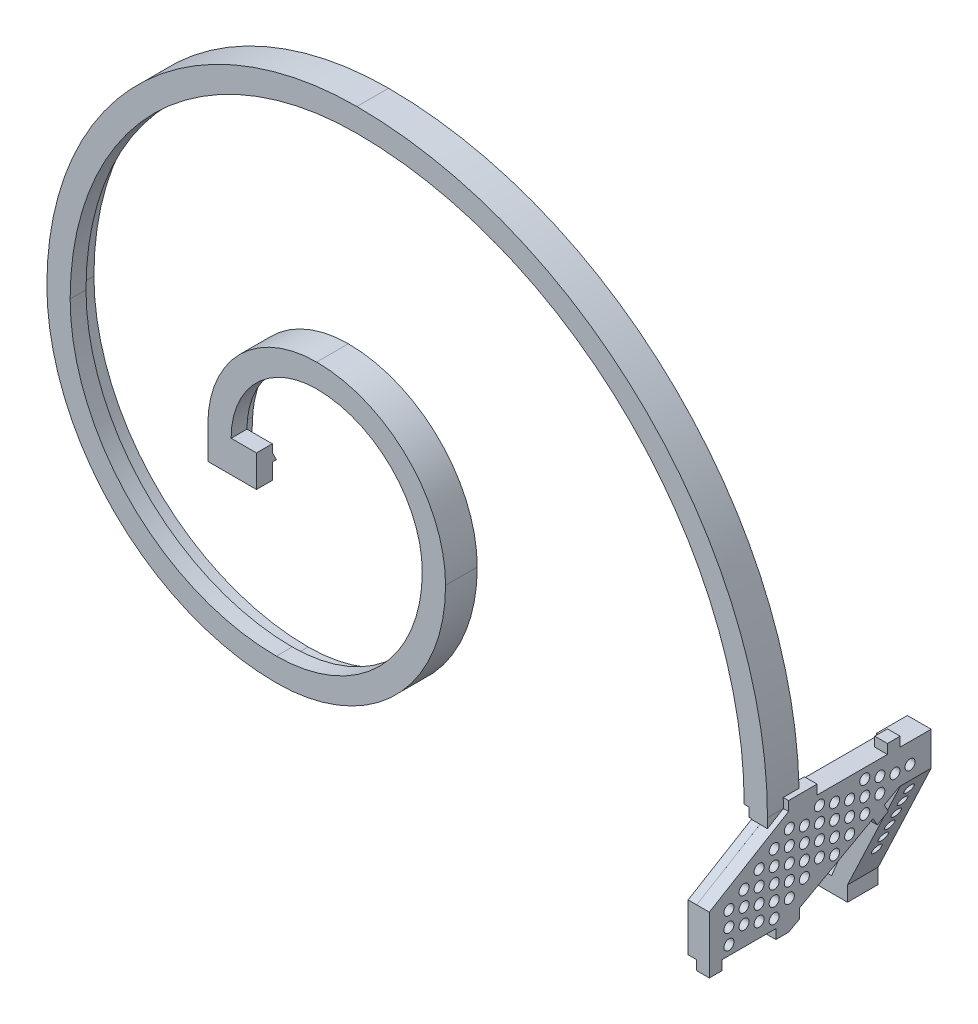
SolidWorks part; units mm, degrees
ref_plane "Front" through (0, 0, 0) normal (0, 0, 1) x (1, 0, 0)
ref_plane "Top" through (0, 0, 0) normal (0, 1, 0) x (1, 0, 0)
ref_plane "Right" through (0, 0, 0) normal (1, 0, 0) x (0, 0, -1)
sketch "Sketch2" plane through (0, 0, 0) normal (0, 0, 1) x (1, 0, 0)
  line L0 (-28.4875, 0) -> (-28.4875, -10)
  line L1 (-28.4875, -10) -> (-31.9875, -10)
  line L2 (-31.9875, -10) -> (-31.9875, 0)
  line L3 (139.9375, -19.05) -> (136.4375, -19.05)
  arc A0 (-28.4875, 0) -> (0, 28.4875) centre (0, 0) cw
  arc A1 (0, 28.4875) -> (34.8375, -6.35) centre (0, -6.35) cw
  arc A2 (34.8375, -6.35) -> (-12.7, -53.8875) centre (-12.7, -6.35) cw
  arc A3 (-12.7, -53.8875) -> (-79.2875, 12.7) centre (-12.7, 12.7) cw
  arc A4 (-79.2875, 12.7) -> (12.7, 104.6875) centre (12.7, 12.7) cw
  arc A5 (12.7, 104.6875) -> (136.4375, -19.05) centre (12.7, -19.05) cw
  arc A6 (-31.9875, 0) -> (0, 31.9875) centre (0, 0) cw
  arc A7 (0, 31.9875) -> (38.3375, -6.35) centre (0, -6.35) cw
  arc A8 (38.3375, -6.35) -> (-12.7, -57.3875) centre (-12.7, -6.35) cw
  arc A9 (-12.7, -57.3875) -> (-82.7875, 12.7) centre (-12.7, 12.7) cw
  arc A10 (-82.7875, 12.7) -> (12.7, 108.1875) centre (12.7, 12.7) cw
  arc A11 (12.7, 108.1875) -> (139.9375, -19.05) centre (12.7, -19.05) cw
extrude "Extrude2" add sketch "Sketch2" along normal blind 5
sketch "Sketch3" plane through (0, 0, 5) normal (0, 0, 1) x (1, 0, 0)
  line L0 (-26.9875, 0) -> (-26.9875, -10)
  line L1 (-26.9875, -10) -> (-31.9875, -10)
  line L2 (134.9375, -19.05) -> (139.9375, -19.05)
  line L3 (-31.9875, -10) -> (-31.9875, 0)
  arc A0 (-31.9875, 0) -> (0, 31.9875) centre (0, 0) cw
  arc A1 (-26.9875, 0) -> (0, 26.9875) centre (0, 0) cw
  arc A2 (0, 26.9875) -> (33.3375, -6.35) centre (0, -6.35) cw
  arc A3 (0, 31.9875) -> (38.3375, -6.35) centre (0, -6.35) cw
  arc A5 (33.3375, -6.35) -> (-12.7, -52.3875) centre (-12.7, -6.35) cw
  arc A6 (-12.7, -52.3875) -> (-77.7875, 12.7) centre (-12.7, 12.7) cw
  arc A7 (-77.7875, 12.7) -> (12.7, 103.1875) centre (12.7, 12.7) cw
  arc A8 (12.7, 103.1875) -> (134.9375, -19.05) centre (12.7, -19.05) cw
  arc A9 (38.3375, -6.35) -> (-12.7, -57.3875) centre (-12.7, -6.35) cw
  arc A10 (-12.7, -57.3875) -> (-82.7875, 12.7) centre (-12.7, 12.7) cw
  arc A11 (-82.7875, 12.7) -> (-12.7, -57.3875) centre (-12.7, 12.7) ccw construction
  arc A12 (-82.7875, 12.7) -> (12.7, 108.1875) centre (12.7, 12.7) cw
  arc A13 (12.7, 108.1875) -> (139.9375, -19.05) centre (12.7, -19.05) cw
extrude "Extrude3" add sketch "Sketch3" along normal blind 5
sketch "Sketch4" plane through (-28.4875, 0, 0) normal (1, 0, 0) x (0, 0, -1)
  line L0 (-5, -2.4) -> (-1.2, -10)
  line L1 (-5, -19.05) -> (-5, 104.6875) construction
  line L2 (-5, -10) -> (0, -10) construction
  line L3 (-1.2, -10) -> (-5, -10)
  line L4 (-5, -10) -> (-5, -2.4)
extrude "Extrude4" add sketch "Sketch4" along normal blind 9.5
sketch "Sketch6" plane through (-18.9875, 0, 0) normal (1, 0, 0) x (0, 0, -1)
  line L0 (-5, -5) -> (-3.7, -5)
  line L1 (-5, -19.05) -> (-5, 104.6875) construction
  line L2 (-1.2, -10) -> (-5, -2.4) construction
  line L3 (-3.7, -5) -> (-1.2, -10)
  line L4 (-1.2, -10) -> (-5, -10)
  line L5 (-5, -10) -> (-5, -5)
extrude "Cut-Extrude1" cut sketch "Sketch6" against normal blind 8
sketch "Sketch7" plane through (-26.9875, 0, 0) normal (1, 0, 0) x (0, 0, -1)
  line L0 (-5, 0) -> (-10, 0)
  line L1 (-10, 0) -> (-10, -10)
  line L2 (-10, -10) -> (-5, -10)
  line L3 (-5, -19.05) -> (-5, 104.6875) construction
  line L4 (-5, -10) -> (-5, 0)
extrude "Extrude5" add sketch "Sketch7" along normal blind 8
sketch "Sketch8" plane through (0, -19.05, 0) normal (0, -1, 0) x (1, 0, 0)
  line L0 (139.9375, 10) -> (139.9375, 0)
  line L1 (139.9375, 0) -> (136.4375, 0)
  line L2 (136.4375, 0) -> (136.4375, 10)
  line L3 (134.9375, 10) -> (139.9375, 10) construction
  line L4 (136.4375, 10) -> (139.9375, 10)
extrude "Extrude6" add sketch "Sketch8" along normal blind 30
sketch "Sketch9" plane through (0, 0, 10) normal (0, 0, 1) x (1, 0, 0)
  line L0 (136.4375, -19.05) -> (139.9375, -19.05)
  line L1 (139.9375, -19.05) -> (139.9375, -49.05)
  line L2 (139.9375, -49.05) -> (136.4375, -49.05)
  line L3 (136.4375, -49.05) -> (136.4375, -19.05)
extrude "Extrude7" add sketch "Sketch9" along normal blind 20
sketch "Sketch11" plane through (0, 0, 0) normal (0, 0, -1) x (-1, 0, 0)
  line L0 (-139.9375, -19.05) -> (-136.4375, -19.05)
  line L1 (-136.4375, -19.05) -> (-136.4375, -49.05)
  line L2 (-136.4375, -49.05) -> (-139.9375, -49.05)
  line L3 (-139.9375, -49.05) -> (-139.9375, -19.05)
extrude "Extrude8" add sketch "Sketch11" along normal blind 30
sketch "Sketch10" plane through (139.9375, 0, 0) normal (1, 0, 0) x (0, 0, -1)
  line L0 (-5, -49.05) -> (30, -29.7287)
  line L1 (-30, -49.05) -> (-30, -19.05) construction
  line L2 (30, -49.05) -> (-30, -49.05) construction
  line L3 (-30, -34.05) -> (-30, -19.05)
  line L4 (-30, -19.05) -> (-10, -19.05)
  line L5 (-10, -19.05) -> (-10, -22.05)
  line L6 (-10, -22.05) -> (-30, -34.05)
  line L7 (30, -19.05) -> (30, -49.05) construction
  line L8 (30, -29.7287) -> (30, -49.05)
  line L9 (30, -49.05) -> (-5, -49.05)
extrude "Cut-Extrude2" cut sketch "Sketch10" against normal blind 5
sketch "Sketch12" plane through (0, 0, -30) normal (0, 0, -1) x (-1, 0, 0)
  line L0 (-139.9375, -19.05) -> (-136.4375, -19.05)
  line L1 (-136.4375, -19.05) -> (-136.4375, -29.7287)
  line L2 (-139.9375, -19.05) -> (-139.9375, -29.7287)
  line L4 (-136.4375, -29.7287) -> (-139.9375, -29.7287)
extrude "Extrude9" add sketch "Sketch12" along normal blind 10
sketch "Sketch14" plane through (0, 0, 10) normal (0, 0, 1) x (1, 0, 0)
  line L0 (-34.3375, 0) -> (-34.3375, -10)
  line L1 (-31.9875, 0) -> (-31.9875, -10)
  line L2 (-31.9875, 0) -> (-31.9875, -10) construction
  line L3 (-31.9875, -10) -> (-34.3375, -10)
  line L4 (142.2875, -19.0647) -> (142.2875, -34.05)
  line L5 (142.2875, -34.05) -> (139.9375, -34.05)
  line L6 (139.9375, -34.05) -> (139.9375, -19.0647)
  arc A0 (-34.3375, 0) -> (0, 34.3375) centre (0, 0) cw
  arc A1 (0, 34.3375) -> (40.6875, -6.35) centre (0, -6.35) cw
  arc A2 (40.6875, -6.35) -> (-12.7, -59.7375) centre (-12.7, -6.35) cw
  arc A3 (-12.7, -59.7375) -> (-85.1375, 12.7419) centre (-12.7, 12.7) cw
  arc A4 (-31.9875, 0) -> (0, 31.9875) centre (0, 0) cw
  arc A5 (0, 31.9875) -> (38.3375, -6.35) centre (0, -6.35) cw
  arc A6 (38.3375, -6.35) -> (-12.7, -57.3875) centre (-12.7, -6.35) cw
  arc A7 (-12.7, -57.3875) -> (-82.7875, 12.7406) centre (-12.7, 12.7) cw
  arc A8 (-82.7875, 12.7406) -> (12.7, 108.1728) centre (12.7, 12.6853) cw
  arc A9 (-85.1375, 12.7419) -> (12.7, 110.5228) centre (12.7, 12.6853) cw
  arc A10 (12.7, 108.1728) -> (139.9375, -19.0647) centre (12.7, -19.0647) cw
  arc A11 (12.7, 110.5228) -> (142.2875, -19.0647) centre (12.7, -19.0647) cw
extrude "Extrude10" add sketch "Sketch14" against normal blind 10
sketch "Sketch15" plane through (-34.3375, 0, 0) normal (-1, 0, 0) x (0, 0, 1)
  line L0 (0, 14) -> (0, -10)
  line L1 (0, 110.5228) -> (0, 12.7419) construction
  line L2 (0, -10) -> (1.2, -10)
  line L3 (1.2, -10) -> (0, 14)
extrude "Cut-Extrude3" cut sketch "Sketch15" against normal blind 15
sketch "Sketch16" plane through (0, 0, 0) normal (0, 0, -1) x (-1, 0, 0)
  line L0 (28.4875, 0) -> (29.4875, 0)
  line L1 (-137.4375, -19.05) -> (-136.4375, -34.05)
  line L4 (-136.4375, -34.05) -> (-136.4375, -19.05)
  arc A0 (28.4875, 0) -> (0, 28.4875) centre (0, 0) ccw
  arc A1 (0, 28.4875) -> (-34.8375, -6.35) centre (0, -6.35) ccw
  arc A2 (-34.8375, -6.35) -> (12.7, -53.8875) centre (12.7, -6.35) ccw
  arc A3 (12.7, -53.8875) -> (79.2875, 12.7) centre (12.7, 12.7) ccw
  arc A4 (79.2875, 12.7) -> (-12.7, 104.6875) centre (-12.7, 12.7) ccw
  arc A5 (-12.7, 104.6875) -> (-136.4375, -19.05) centre (-12.7, -19.05) ccw
  arc A6 (29.4875, 0) -> (0, 29.4875) centre (0, 0) ccw
  arc A7 (0, 29.4875) -> (-35.8375, -6.35) centre (0, -6.35) ccw
  arc A8 (-35.8375, -6.35) -> (12.7, -54.8875) centre (12.7, -6.35) ccw
  arc A9 (12.7, -54.8875) -> (80.2875, 12.7) centre (12.7, 12.7) ccw
  arc A10 (80.2875, 12.7) -> (-12.7, 105.6875) centre (-12.7, 12.7) ccw
  arc A11 (-12.7, 105.6875) -> (-137.4375, -19.05) centre (-12.7, -19.05) ccw
extrude "Cut-Extrude4" cut sketch "Sketch16" against normal blind 5
sketch "Sketch17" plane through (-28.4875, 0, 0) normal (1, 0, 0) x (0, 0, -1)
  line L0 (-5, 0) -> (-5, -2.4)
  line L1 (-5, -2.4) -> (-1.2, -10)
  line L2 (-1.2, -10) -> (0, -10)
  line L3 (0, -19.0647) -> (0, 110.5228) construction
  line L4 (0, -10) -> (0, 0)
  line L5 (0, 0) -> (-5, 0)
extrude "Cut-Extrude5" cut sketch "Sketch17" against normal blind 1
sketch "Sketch19" plane through (136.4375, 0, 0) normal (-1, 0, 0) x (0, 0, 1)
  line L0 (30, -34.05) -> (5, -19.05) construction
  line L1 (47.1838, -44.127) -> (-33.6162, 4.353) construction
  line L2 (30, -34.05) -> (30, -26.2032) construction
  line L3 (-40, -29.7287) -> (-30, -29.7287) construction
  line L4 (-30.2, -29.7287) -> (-30, -29.7287)
  line L5 (-30, -29.7287) -> (5, -49.05)
  line L6 (5, -49.05) -> (30, -49.05)
  line L7 (30, -49.05) -> (30, -33.8168)
  line L8 (30, -33.8168) -> (5.3887, -19.05)
  line L9 (10, -19.05) -> (5, -19.05) construction
  line L10 (-30.2, -29.7287) -> (-30.2, -19.05)
  line L11 (-40, -19.05) -> (0, -19.05) construction
  line L12 (-30.2, -19.05) -> (5.3887, -19.05)
  point P0 (30, -34.05)
  point P1 (30, -49.05)
  point P3 (5, -49.05)
  point P5 (-30, -29.7287)
  point P13 (30, -33.8168)
  point P15 (-30.2, -29.7287)
  dimension "D1" = 0.2
  dimension "D2" = 0.2
extrude "Extrude11" cut sketch "Sketch19" against normal blind 0.8
sketch "Sketch20" plane through (139.9375, 0, 0) normal (1, 0, 0) x (0, 0, -1)
  line L0 (-30, -49.05) -> (-30, -34.05)
  line L1 (-30, -34.05) -> (-5, -19.0647)
  line L2 (0, -19.0647) -> (-10, -19.0647) construction
  line L3 (30.2, -19.05) -> (30.2, -16.05)
  line L4 (30.2, -19.05) -> (40, -19.05)
  line L5 (-8.5558, -54.0546) -> (30, -32.8385) construction
  line L6 (-30, -49.05) -> (-30, -52.05)
  line L7 (40, -19.05) -> (40, -29.7287)
  line L8 (40, -29.7287) -> (30, -29.7287)
  line L9 (-30, -52.05) -> (-5, -52.05) construction
  line L10 (-5, -54.8875) -> (-5, -6.35) construction
  line L11 (22.9911, -36.6953) -> (21.6806, -34.3214)
  line L12 (30.2, -16.05) -> (-5, -16.05) construction
  line L13 (-5, -19.05) -> (-5, 105.6875) construction
  line L14 (-5, -16.05) -> (-5, -19.0647)
  line L15 (26.4955, -34.7669) -> (25.1824, -32.3882)
  line L16 (0, -19.0647) -> (0, 110.5228) construction
  line L17 (-30, -52.05) -> (-26, -52.05)
  line L18 (-26, -52.05) -> (-26, -49.05)
  line L19 (-5, -49.05) -> (-30, -49.05) construction
  line L20 (-5, -52.05) -> (-9, -52.05)
  line L21 (-9, -52.05) -> (-9, -49.05)
  line L22 (-5, -52.05) -> (-1.4755, -50.1585)
  line L23 (-1.4755, -50.1585) -> (-1.4755, -47.1043)
  line L24 (30, -29.7287) -> (-5, -49.05) construction
  line L25 (25.1824, -32.3882) -> (30, -29.7287)
  line L26 (-1.4755, -47.1043) -> (21.6806, -34.3214)
  line L27 (22.9911, -36.6953) -> (26.4955, -34.7669)
  line L28 (-9, -49.05) -> (-26, -49.05)
  line L29 (30.2, -16.05) -> (26.2, -16.05)
  line L30 (26.2, -16.05) -> (26.2, -19.05)
  line L31 (40, -19.05) -> (0, -19.05) construction
  line L32 (-5, -16.05) -> (4, -16.05)
  line L33 (4, -16.05) -> (4, -19.05)
  line L34 (4, -19.05) -> (26.2, -19.05)
  point P12 (26.2, -16.05)
  point P13 (22.9911, -36.6953)
  point P21 (26.4955, -34.7669)
  point P26 (4, -16.05)
  point P29 (-26, -52.05)
  point P30 (-1.4755, -50.1585)
  point P33 (-9, -52.05)
  dimension "D1" = 4
  dimension "MLK" = 4
  dimension "D2" = 4
  dimension "D3" = 4
  dimension "D4" = 4
  dimension "D5" = 4
  dimension "D6" = 4
extrude "Extrude12" add sketch "Sketch20" along normal blind 4
sketch "Sketch21" plane through (0, 0, -40) normal (0, 0, -1) x (-1, 0, 0)
  line L0 (-136.4375, -19.05) -> (-136.4375, -29.7287)
  line L1 (-136.4375, -29.7287) -> (-122.24, -65.09)
  line L2 (-122.24, -65.09) -> (-115.7125, -65.0875)
  line L3 (-127.24, -65.0875) -> (-143.9375, -29.7287)
  line L4 (-143.9375, -29.7287) -> (-143.9375, -19.05)
  line L5 (-143.9375, -19.05) -> (-136.4375, -19.05)
  line L6 (-115.7125, -65.0875) -> (-115.7125, -69.85)
  line L7 (-115.7125, -69.85) -> (-138.1125, -69.85) construction
  line L8 (-127.24, -65.0875) -> (-127.24, -69.85)
  line L9 (-127.24, -69.85) -> (-115.7125, -69.85)
  point P0 (-136.4375, -29.7287)
  point P1 (-136.4375, -19.05)
  point P3 (-122.24, -65.09)
  point P5 (-127.24, -65.0875)
  point P8 (-115.7125, -65.0875)
  point P15 (-115.7125, -69.85)
extrude "Extrude13" add sketch "Sketch21" against normal blind 9.7
sketch "Sketch22" plane through (143.9375, 0, 0) normal (1, 0, 0) x (0, 0, -1)
  circle A0 centre (-23.8125, -36.5125) radius 1.5875
  circle A1 centre (-19.05, -33.3375) radius 1.5875
  circle A2 centre (-14.2875, -30.1625) radius 1.5875
  circle A3 centre (-9.525, -26.9875) radius 1.5875
  circle A4 centre (-4.7625, -23.8125) radius 1.5875
  circle A5 centre (-23.8125, -41.275) radius 1.5875
  circle A6 centre (-19.05, -38.1) radius 1.5875
  circle A7 centre (-14.2875, -34.925) radius 1.5875
  circle A8 centre (-9.525, -31.75) radius 1.5875
  circle A9 centre (-4.7625, -28.575) radius 1.5875
  circle A10 centre (0, -25.4) radius 1.5875
  circle A11 centre (4.7625, -26.9875) radius 1.5875
  circle A12 centre (-23.8125, -46.0375) radius 1.5875
  circle A13 centre (-19.05, -42.8625) radius 1.5875
  circle A14 centre (-14.2875, -39.6875) radius 1.5875
  circle A15 centre (-9.525, -36.5125) radius 1.5875
  circle A16 centre (-4.7625, -33.3375) radius 1.5875
  circle A17 centre (0, -30.1625) radius 1.5875
  circle A18 centre (-14.2875, -44.45) radius 1.5875
  circle A19 centre (-9.525, -41.275) radius 1.5875
  circle A20 centre (-4.7625, -38.1) radius 1.5875
  circle A21 centre (0, -34.925) radius 1.5875
  circle A22 centre (4.7625, -31.75) radius 1.5875
  circle A23 centre (-9.525, -46.0375) radius 1.5875
  circle A24 centre (-4.7625, -42.8625) radius 1.5875
  circle A25 centre (0, -39.6875) radius 1.5875
  circle A26 centre (4.7625, -36.5125) radius 1.5875
  circle A27 centre (9.525, -33.3375) radius 1.5875
  circle A28 centre (9.525, -28.575) radius 1.5875
  circle A29 centre (9.525, -23.8125) radius 1.5875
  circle A30 centre (4.7625, -22.225) radius 1.5875
  circle A31 centre (14.2875, -30.1625) radius 1.5875
  circle A32 centre (14.2875, -25.4) radius 1.5875
  circle A33 centre (19.05, -26.9875) radius 1.5875
  circle A34 centre (19.05, -22.225) radius 1.5875
  circle A35 centre (9.525, -38.1) radius 1.5875
  circle A36 centre (14.2875, -34.925) radius 1.5875
  circle A37 centre (19.05, -31.75) radius 1.5875
  circle A38 centre (23.8125, -28.575) radius 1.5875
  circle A39 centre (23.8125, -23.8125) radius 1.5875
  circle A40 centre (28.575, -25.4) radius 1.5875
  circle A41 centre (33.3375, -25.4) radius 1.5875
extrude "Extrude14" cut sketch "Sketch22" against normal blind 4
sketch "Sketch23" plane through (129.1709, -60.9985, 0) normal (0.9042, -0.427, 0) x (0, 0, -1)
  circle A0 centre (34.925, 30.1625) radius 1.5875
  circle A1 centre (34.925, 25.4) radius 1.5875
  circle A2 centre (34.925, 20.6375) radius 1.5875
  circle A3 centre (34.925, 15.875) radius 1.5875
  circle A4 centre (34.925, 11.1125) radius 1.5875
  circle A5 centre (34.925, 6.35) radius 1.5875
extrude "Extrude15" cut sketch "Sketch23" against normal blind 2
equation "\"D1@Sketch20\" = \"MLK\""
equation "\"D2@Sketch20\" = \"MLK\""
equation "\"D3@Sketch20\" = \"MLK\""
equation "\"D4@Sketch20\" = \"MLK\""
equation "\"D5@Sketch20\" = \"MLK\""
equation "\"D6@Sketch20\" = \"MLK\""
